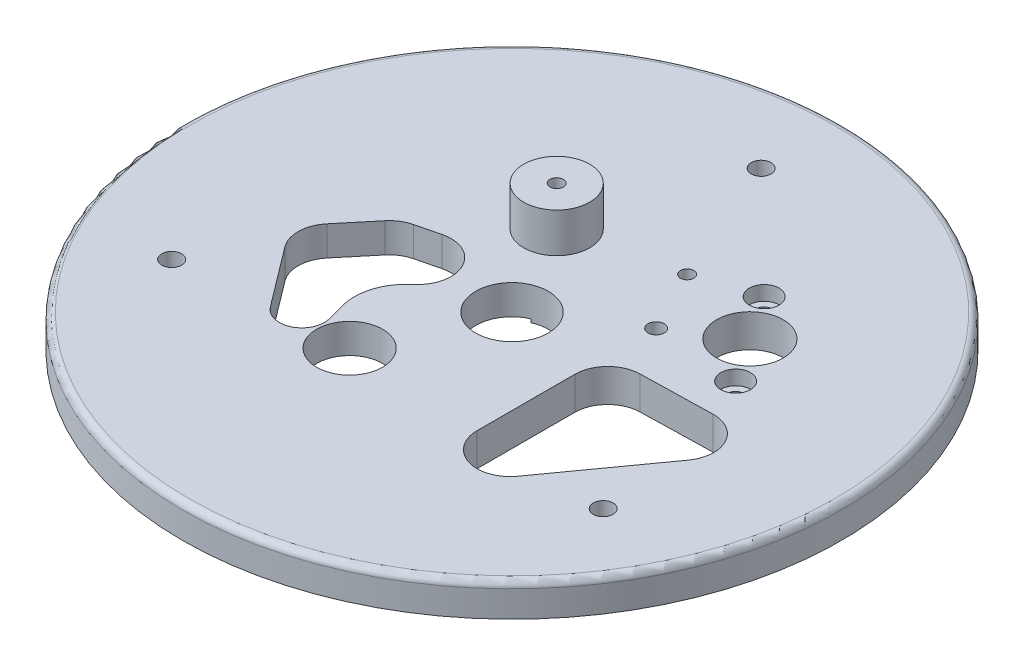
SolidWorks part; units mm, degrees
ref_plane "Front Plane" through (0, 0, 0) normal (0, 0, 1) x (1, 0, 0)
ref_plane "Top Plane" through (0, 0, 0) normal (0, 1, 0) x (1, 0, 0)
ref_plane "Right Plane" through (0, 0, 0) normal (1, 0, 0) x (0, 0, -1)
sketch "Sketch1" plane through (0, 0, 0) normal (0, 1, 0) x (1, 0, 0)
  circle A0 centre (0, 0) radius 50
  circle A9 centre (-7.5739, -17.0603) radius 5
  point P4 (4.2153, -18.1838)
  point P5 (-7.5739, -17.0603)
  dimension "D1" = 100
  dimension "D5" = 10
  dimension "D6" = 18.666
extrude "Boss-Extrude1" add sketch "Sketch1" along normal blind 5
sketch "Sketch2" plane through (0, 5, 0) normal (0, 1, 0) x (1, 0, 0)
  line L0 (26.0308, 7.8992) -> (17.0876, 21.1664) construction
  line L1 (26.0308, 7.8992) -> (13.0624, 8.8052) construction
  line L2 (13.0624, 8.8052) -> (17.0876, 21.1664) construction
  line L3 (13.0624, 8.8052) -> (21.5592, 14.5328) construction
  circle A0 centre (26.0308, 7.8992) radius 1.2
  circle A1 centre (17.0876, 21.1664) radius 1.2
  circle A2 centre (13.0624, 8.8052) radius 1.225
  circle A3 centre (21.5592, 14.5328) radius 5.05
  circle A4 centre (8.3208, 18.2484) radius 1.015
  circle A5 centre (21.5592, 14.5328) radius 13.75 construction
  circle A6 centre (0, 0) radius 30 construction
  circle A7 centre (8.3208, 18.2484) radius 11.25 construction
  point P9 (21.5592, 14.5328)
  point P16 (18.2424, 12.2969)
  dimension "D1" = 2.4
  dimension "D2" = 10.1
  dimension "D3" = 2.45
  dimension "D7" = 2.03
  dimension "D9" = 60
  dimension "D10" = 22.5
  dimension "D4" = 16
  dimension "D5" = 13
  dimension "D6" = 26
  dimension "D8" = 13.75
extrude "Cut-Extrude1" cut sketch "Sketch2" against normal blind 10
sketch "Sketch4" plane through (0, 5, 0) normal (0, 1, 0) x (1, 0, 0)
  circle A0 centre (0, 0) radius 31 construction
  dimension "D1" = 62
sketch "Sketch5" plane through (0, 5, 0) normal (0, 1, 0) x (1, 0, 0)
  line L0 (-7.5531, 14.3315) -> (0, 0) construction
  circle A0 centre (-7.5531, 14.3315) radius 5
  circle A1 centre (8.3208, 18.2484) radius 1 construction
  circle A2 centre (-7.5531, 14.3315) radius 1.015
  circle A3 centre (-7.5531, 14.3315) radius 14 construction
  dimension "D2" = 10
  dimension "D3" = 2.03
  dimension "D4" = 28
  dimension "D1" = 16.35
  dimension "D5" = 16.2
extrude "Boss-Extrude2" add sketch "Sketch5" along normal blind 6
sketch "Sketch9" plane through (0, 0, 0) normal (0, -1, 0) x (1, 0, 0)
  circle A0 centre (8.3208, -18.2484) radius 2.3573
extrude "Boss-Extrude4" add sketch "Sketch9" against normal blind 1
fillet "Fillet1" radius 1 1 edges at (0, 5, 50)
sketch "Sketch10" plane through (0, 5, 0) normal (0, 1, 0) x (1, 0, 0)
  line L0 (-32.7358, -18.9) -> (0, 0) construction
  line L1 (0, 37.8) -> (0, 0) construction
  line L2 (32.7358, -18.9) -> (0, 0) construction
  circle A0 centre (0, 37.8) radius 1.5
  circle A1 centre (-32.7358, -18.9) radius 1.5
  circle A2 centre (32.7358, -18.9) radius 1.5
  dimension "D2" = 3
  dimension "D3" = 120
  dimension "D1" = 37.8
  dimension "D4" = 120
extrude "Cut-Extrude3" cut sketch "Sketch10" against normal blind 16 and the other way blind 2.2
sketch "Sketch12" plane through (0, 0, 0) normal (0, -1, 0) x (1, 0, 0)
  line L0 (-21.3138, 24.7621) -> (-34.5388, 1.8558)
  line L1 (-32.7087, -4.9744) -> (-14.0892, -15.7244)
  line L2 (-7.259, -13.8942) -> (5.966, 9.0121)
  line L3 (5.966, 9.0121) -> (-21.3138, 24.7621) construction
  line L4 (-7.6739, 16.8871) -> (-7.5739, 17.0603) construction
  line L5 (-32.7358, 18.9) -> (-43.3013, 25) construction
  line L6 (-26.7077, 15.4197) -> (-32.7358, 18.9) construction
  line L7 (-41.991, 27.2694) -> (-45.8292, 20.6215) construction
  arc A0 (-21.3138, 24.7621) -> (5.966, 9.0121) centre (-7.6739, 16.8871) cw
  arc A1 (-7.259, -13.8942) -> (-14.0892, -15.7244) centre (-11.5892, -11.3942) cw
  arc A2 (-34.5388, 1.8558) -> (-32.7087, -4.9744) centre (-30.2087, -0.6442) ccw
  circle A3 centre (-7.5739, 17.0603) radius 4.1018 construction
  circle A4 centre (-7.5739, 17.0603) radius 5 construction
  circle A5 centre (0, 0) radius 50 construction
  point P4 (0.2011, 30.527)
  point P9 (-9.759, -18.2244)
  point P12 (-37.0388, -2.4744)
  dimension "D3" = 5
  dimension "D4" = 0.2
  dimension "D1" = 47.2
  dimension "D2" = 31.5
extrude "Cut-Extrude6" cut sketch "Sketch12" against normal blind 0.5
sketch "Sketch13" plane through (0, 5, 0) normal (0, 1, 0) x (1, 0, 0)
  line L0 (32.8168, -6.0717) -> (21.985, -21.1386)
  line L1 (12.9252, -18.2178) -> (12.9317, -3.4072)
  line L2 (17.8133, 1.5892) -> (28.6387, 1.8455)
  arc A0 (21.985, -21.1386) -> (12.9252, -18.2178) centre (17.9252, -18.22) cw
  arc A1 (17.8133, 1.5892) -> (12.9317, -3.4072) centre (17.9317, -3.4094) ccw
  arc A2 (28.6387, 1.8455) -> (32.8168, -6.0717) centre (28.7571, -3.1531) cw
  dimension "D1" = 5
extrude "Cut-Extrude7" cut sketch "Sketch13" against normal blind 10
sketch "Sketch16" plane through (0, 0.5, 0) normal (0, -1, 0) x (1, 0, 0)
  line L0 (-12.9842, 14.7056) -> (-13.7197, 11.9588)
  line L1 (-11.5496, 4.2419) -> (-10.8428, 3.5689)
  line L2 (-15.4939, -4.9052) -> (-19.0041, -4.0349)
  line L3 (-21.6454, -2.3787) -> (-25.6533, 2.4414)
  line L4 (-25.8003, 8.6495) -> (-19.0121, 17.6471)
  arc A0 (-25.6533, 2.4414) -> (-25.8003, 8.6495) centre (-21.8088, 5.6382) cw
  arc A1 (-19.0041, -4.0349) -> (-21.6454, -2.3787) centre (-17.8008, 0.8181) cw
  arc A2 (-15.4939, -4.9052) -> (-10.8428, 3.5689) centre (-14.2907, -0.0522) ccw
  arc A3 (-13.7197, 11.9588) -> (-11.5496, 4.2419) centre (-6.1357, 9.9279) ccw
  arc A4 (-12.9842, 14.7056) -> (-19.0121, 17.6471) centre (-16.2845, 15.5894) ccw
  dimension "D1" = 5
extrude "Cut-Extrude9" cut sketch "Sketch16" against normal blind 10 and the other way blind 10
sketch "Sketch17" plane through (0, 0.5, 0) normal (0, -1, 0) x (1, 0, 0)
  circle A0 centre (0, 0) radius 5.5
  dimension "D1" = 11
extrude "Cut-Extrude10" cut sketch "Sketch17" against normal blind 10 and the other way blind 10
sketch "Sketch18" plane through (0, 5, 0) normal (0, 1, 0) x (1, 0, 0)
  circle A0 centre (17.0876, 21.1664) radius 2.25
  circle A1 centre (26.0308, 7.8992) radius 2.25
  dimension "D1" = 4.5
extrude "Cut-Extrude11" cut sketch "Sketch18" against normal blind 2.2
